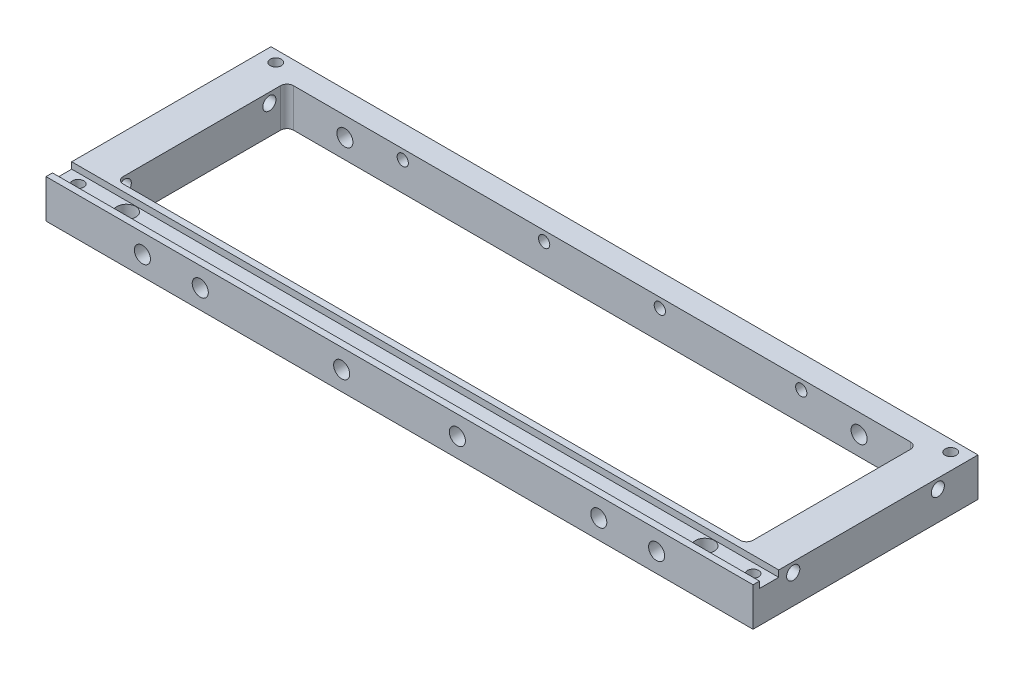
SolidWorks part; units mm, degrees
ref_plane "Front Plane" through (0, 0, 0) normal (0, 0, 1) x (1, 0, 0)
ref_plane "Top Plane" through (0, 0, 0) normal (0, 1, 0) x (1, 0, 0)
ref_plane "Right Plane" through (0, 0, 0) normal (1, 0, 0) x (0, 0, -1)
sketch "Sketch1" plane through (0, 0, 0) normal (0, 1, 0) x (1, 0, 0)
  line L1 (0, 0) -> (110, 0)
  line L2 (0, 0) -> (0, 35)
  line L3 (0, 35) -> (110, 35)
  line L4 (110, 0) -> (110, 35)
  dimension "D1" = 110
  dimension "D2" = 35
extrude "Boss-Extrude1" add sketch "Sketch1" along normal blind 6
sketch "Sketch2" plane through (0, 6, 0) normal (0, 1, 0) x (1, 0, 0)
  line L0 (0, 35) -> (0, 0) construction
  line L1 (6, 31.5) -> (104, 31.5)
  line L2 (6, 31.5) -> (6, 5)
  line L3 (6, 5) -> (104, 5)
  line L4 (104, 31.5) -> (104, 5)
  line L5 (110, 0) -> (110, 35) construction
  line L6 (110, 35) -> (0, 35) construction
  line L7 (0, 0) -> (110, 0) construction
  dimension "D1" = 6
  dimension "D2" = 6
  dimension "D3" = 3.5
  dimension "D4" = 5
extrude "Cut-Extrude1" cut sketch "Sketch2" against normal blind 6
sketch "Sketch3" plane through (0, 6, 0) normal (0, 1, 0) x (1, 0, 0)
  line L0 (0, 35) -> (0, 0) construction
  line L1 (0, 1) -> (110, 1)
  line L2 (0, 1) -> (0, 4)
  line L3 (0, 4) -> (110, 4)
  line L4 (110, 1) -> (110, 4)
  line L5 (110, 0) -> (110, 35) construction
  line L6 (0, 0) -> (110, 0) construction
  line L7 (6, 5) -> (104, 5) construction
  dimension "D1" = 1
  dimension "D2" = 1
extrude "Cut-Extrude2" cut sketch "Sketch3" against normal blind 1
hole_wizard "CBORE for M2.5 SHCS1" positions "Sketch10" profile "Sketch9" counterbore size "M2.5" standard "ANSI Metric" end condition through all
sketch "Sketch10" plane through (0, 0, 0) normal (0, -1, 0) x (-1, 0, 0)
  line L0 (0, 0) -> (-110, 0) construction
  line L1 (0, 35) -> (0, 0) construction
  line L2 (-110, 0) -> (-110, 35) construction
  point P0 (-100, 2.5)
  point P2 (-10, 2.5)
  dimension "D1" = 2.5
  dimension "D2" = 2.5
  dimension "D3" = 10
  dimension "D4" = 10
sketch "Sketch9" plane through (100, 0, -2.5) normal (1, 0, 0) x (0, 0, -1)
  line L0 (0, 0) -> (0, 6)
  line L1 (0, 6) -> (1.45, 6)
  line L3 (1.45, 6) -> (1.45, 2.5)
  line L4 (1.45, 2.5) -> (2.3, 2.5)
  line L5 (2.3, 2.5) -> (2.3, 0)
  line L7 (2.3, 0) -> (0, 0)
  line L11 (0, -6.35) -> (0, 107.95) construction
  dimension "Thru Hole Dia." = 2.9
  dimension "Thru Hole Depth" = 6
  dimension "C'Bore Dia." = 4.6
  dimension "C'Bore Depth" = 2.5
fillet "Fillet1" radius 1 4 edges at (104, 3, -5) (6, 3, -5) (6, 3, -31.5) (104, 3, -31.5)
hole_wizard "Tap Drill for M2.2x0.45 Tap1" positions "Sketch13" profile "Sketch12" hole size "M2.2x0.45" standard "ANSI Metric" end condition through all
sketch "Sketch13" plane through (0, 0, 0) normal (0, -1, 0) x (-1, 0, 0)
  line L0 (0, 0) -> (-110, 0) construction
  line L1 (0, 35) -> (0, 0) construction
  line L2 (-110, 0) -> (-110, 35) construction
  line L3 (-110, 35) -> (0, 35) construction
  point P0 (-2.5, 2.5)
  point P2 (-107.5, 2.5)
  point P4 (-107.5, 33.25)
  point P6 (-2.5, 33.25)
  dimension "D1" = 2.5
  dimension "D2" = 2.5
  dimension "D3" = 2.5
  dimension "D4" = 2.5
  dimension "D5" = 2.5
  dimension "D6" = 2.5
  dimension "D7" = 1.75
  dimension "D8" = 1.75
sketch "Sketch12" plane through (2.5, 0, -2.5) normal (1, 0, 0) x (0, 0, -1)
  line L0 (0, 0) -> (0, 6)
  line L1 (0, 6) -> (0.875, 6)
  line L2 (0.875, 6) -> (0.875, 0)
  line L5 (0.875, 0) -> (0, 0)
  line L11 (0, -6.35) -> (0, 107.95) construction
  dimension "Thru Hole Dia." = 1.75
  dimension "Thru Hole Depth" = 6
hole_wizard "Tap Drill for M3x0.5 Tap1" positions "Sketch14" profile "Sketch16" hole size "M3x0.5" standard "ANSI Metric"
sketch "Sketch14" plane through (0, 0, 0) normal (0, 0, 1) x (1, 0, 0)
  line L0 (0, 6) -> (0, 0) construction
  line L1 (110, 6) -> (110, 0) construction
  point P0 (15, 3)
  point P2 (24, 3)
  point P4 (46, 3)
  point P6 (64, 3)
  point P8 (86, 3)
  point P10 (95, 3)
  dimension "D1" = 15
  dimension "D2" = 9
  dimension "D3" = 46
  dimension "D4" = 18
  dimension "D5" = 15
  dimension "D6" = 9
sketch "Sketch16" plane through (15, 3, 0) normal (1, 0, 0) x (0, -1, 0)
  line L0 (0, 0) -> (0, 6.7511)
  line L1 (0, 6.7511) -> (1.25, 6)
  line L2 (1.25, 6) -> (1.25, 0)
  line L5 (1.25, 0) -> (0, 0)
  line L10 (0, 6.7511) -> (-1.25, 6) construction
  line L11 (0, -6.35) -> (0, 107.95) construction
  dimension "Hole Dia." = 2.5
  dimension "Hole Depth" = 6
  dimension "Drill Angle" = 118
sketch "Sketch17" plane through (0, 0, 0) normal (0, -1, 0) x (1, 0, 0)
  line L0 (0, 0) -> (110, 0) construction
  line L1 (50, -4) -> (60, -4)
  line L2 (50, -4) -> (50, -1)
  line L3 (50, -1) -> (60, -1)
  line L4 (60, -4) -> (60, -1)
  line L5 (28.5, -4) -> (42.5, -4)
  line L6 (28.5, -4) -> (28.5, -1)
  line L7 (28.5, -1) -> (42.5, -1)
  line L8 (42.5, -4) -> (42.5, -1)
  line L9 (67.5, -1) -> (81.5, -1)
  line L10 (67.5, -1) -> (67.5, -4)
  line L11 (67.5, -4) -> (81.5, -4)
  line L12 (81.5, -1) -> (81.5, -4)
  line L13 (110, 0) -> (110, -35) construction
  dimension "D1" = 10
  dimension "D2" = 3
  dimension "D3" = 3
  dimension "D4" = 3
  dimension "D5" = 14
  dimension "D6" = 14
  dimension "D7" = 7.5
  dimension "D8" = 7.5
  dimension "D9" = 1
  dimension "D10" = 1
  dimension "D11" = 1
  dimension "D12" = 28.5
extrude "Cut-Extrude3" cut sketch "Sketch17" against normal blind 4
fillet "Fillet2" radius 0.5 12 edges at (67.5, 2, -1) (81.5, 2, -1) (81.5, 2, -4) (67.5, 2, -4) (50, 2, -4) (50, 2, -1) (60, 2, -1) (60, 2, -4) (42.5, 2, -4) (42.5, 2, -1) (28.5, 2, -4) (28.5, 2, -1)
hole_wizard "Tap Drill for M3x0.5 Tap2" positions "Sketch18" profile "Sketch19" hole size "M3x0.5" standard "ANSI Metric"
sketch "Sketch18" plane through (0, 0, -35) normal (0, 0, -1) x (-1, 0, 0)
  line L2 (-110, 6) -> (-110, 0) construction
  line L3 (-110, 6) -> (0, 6) construction
  point P2 (-15, 3)
  point P7 (-95, 3)
  dimension "D1" = 15
  dimension "D2" = 3
sketch "Sketch19" plane through (15, 3, -35) normal (1, 0, 0) x (0, 1, 0)
  line L0 (0, 0) -> (0, 6.7511)
  line L1 (0, 6.7511) -> (1.25, 6)
  line L2 (1.25, 6) -> (1.25, 0)
  line L5 (1.25, 0) -> (0, 0)
  line L10 (0, 6.7511) -> (-1.25, 6) construction
  line L11 (0, -6.35) -> (0, 107.95) construction
  dimension "Hole Dia." = 2.5
  dimension "Hole Depth" = 6
  dimension "Drill Angle" = 118
hole_wizard "Tap Drill for M2.2x0.45 Tap2" positions "Sketch20" profile "Sketch21" hole size "M2.2x0.45" standard "ANSI Metric"
sketch "Sketch20" plane through (0, 0, -35) normal (0, 0, -1) x (-1, 0, 0)
  line L0 (-110, 6) -> (0, 6) construction
  line L1 (-110, 6) -> (-110, 0) construction
  circle A0 centre (-15, 3) radius 1.25 construction
  circle A1 centre (-95, 3) radius 1.25 construction
  point P0 (-24, 4.5)
  point P2 (-46, 4.5)
  point P4 (-64, 4.5)
  point P6 (-86, 4.5)
  point P20 (-110, 3)
  dimension "D1" = 1.5
  dimension "D2" = 9
  dimension "D3" = 1.5
  dimension "D4" = 1.5
  dimension "D5" = 18
  dimension "D6" = 46
  dimension "D7" = 1.5
  dimension "D8" = 9
sketch "Sketch21" plane through (24, 4.5, -35) normal (1, 0, 0) x (0, 1, 0)
  line L0 (0, 0) -> (0, 6.5258)
  line L1 (0, 6.5258) -> (0.875, 6)
  line L2 (0.875, 6) -> (0.875, 0)
  line L5 (0.875, 0) -> (0, 0)
  line L10 (0, 6.5258) -> (-0.875, 6) construction
  line L11 (0, -6.35) -> (0, 107.95) construction
  dimension "Hole Dia." = 1.75
  dimension "Hole Depth" = 6
  dimension "Drill Angle" = 118
hole_wizard "Tap Drill for M2.5x0.45 Tap2" positions "Sketch22" profile "Sketch24" hole size "M2.5x0.45" standard "ANSI Metric" end condition through all
sketch "Sketch22" plane through (110, 0, 0) normal (1, 0, 0) x (0, 0, -1)
  line L0 (4, 6) -> (35, 6) construction
  line L1 (0, 6) -> (0, 0) construction
  line L2 (35, 6) -> (35, 0) construction
  point P0 (6.25, 4.5)
  point P2 (28.75, 4.5)
  dimension "D1" = 1.5
  dimension "D2" = 1.5
  dimension "D3" = 6.25
  dimension "D4" = 6.25
sketch "Sketch24" plane through (110, 4.5, -6.25) normal (0, 1, 0) x (0, 0, -1)
  line L0 (0, 0) -> (0, 110)
  line L1 (0, 110) -> (1.025, 110)
  line L2 (1.025, 110) -> (1.025, 0)
  line L5 (1.025, 0) -> (0, 0)
  line L11 (0, -6.35) -> (0, 107.95) construction
  dimension "Thru Hole Dia." = 2.05
  dimension "Thru Hole Depth" = 110
